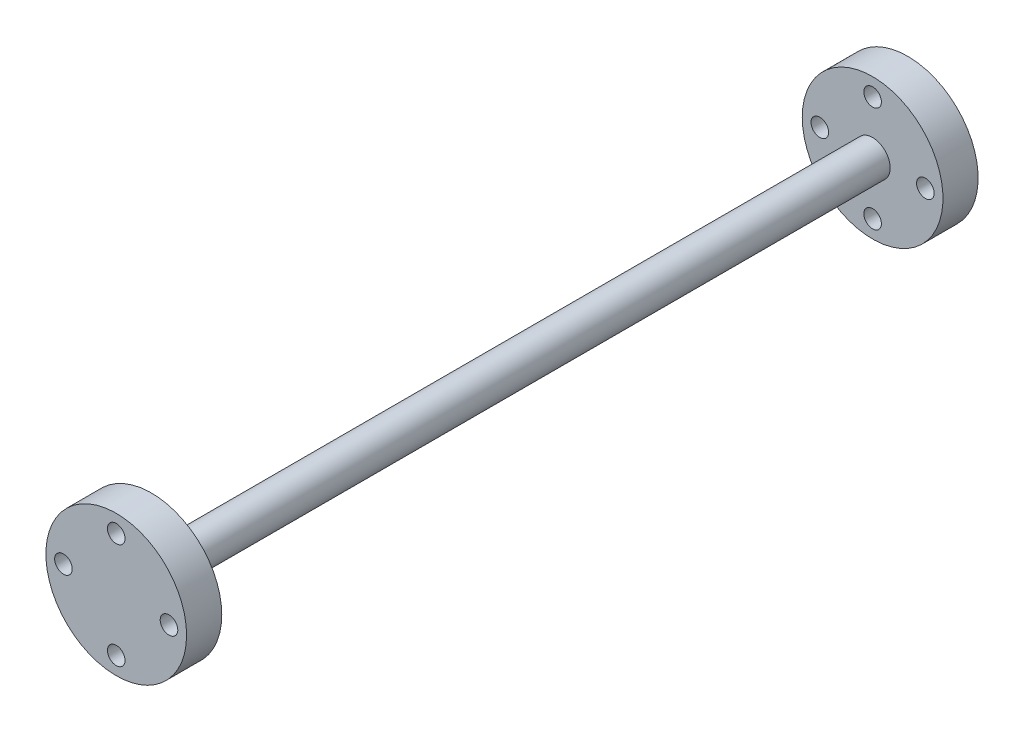
SolidWorks part; units mm, degrees
ref_plane "Front Plane" through (0, 0, 0) normal (0, 0, 1) x (1, 0, 0)
ref_plane "Top Plane" through (0, 0, 0) normal (0, 1, 0) x (1, 0, 0)
ref_plane "Right Plane" through (0, 0, 0) normal (1, 0, 0) x (0, 0, -1)
sketch "Sketch1" plane through (0, 0, 0) normal (0, 0, 1) x (1, 0, 0)
  circle A0 centre (0, 0) radius 5
  dimension "D1" = 10
extrude "Boss-Extrude1" add sketch "Sketch1" along normal blind 105 and the other way blind 100
sketch "Sketch2" plane through (0, 0, 105) normal (0, 0, 1) x (1, 0, 0)
  circle A0 centre (0, 0) radius 20
  circle A1 centre (0, 15) radius 2.5
  circle A2 centre (15, 0) radius 2.5
  circle A3 centre (0, -15) radius 2.5
  circle A4 centre (-15, 0) radius 2.5
  point P14 (0, 0)
  dimension "D1" = 40
  dimension "D2" = 5
  dimension "D4" = 4
  dimension "D3" = 15
extrude "Boss-Extrude2" add sketch "Sketch2" along normal blind 10
sketch "Sketch3" plane through (0, 0, -100) normal (0, 0, -1) x (-1, 0, 0)
  circle A0 centre (0, 0) radius 20
  circle A1 centre (0, 15) radius 2.5 construction
  circle A2 centre (-15, 0) radius 2.5 construction
  circle A3 centre (0, -15) radius 2.5 construction
  circle A4 centre (15, 0) radius 2.5 construction
  circle A5 centre (0, 15) radius 2.5
  circle A6 centre (-15, 0) radius 2.5
  circle A7 centre (0, -15) radius 2.5
  circle A8 centre (15, 0) radius 2.5
  dimension "D1" = 40
extrude "Boss-Extrude3" add sketch "Sketch3" along normal blind 10
